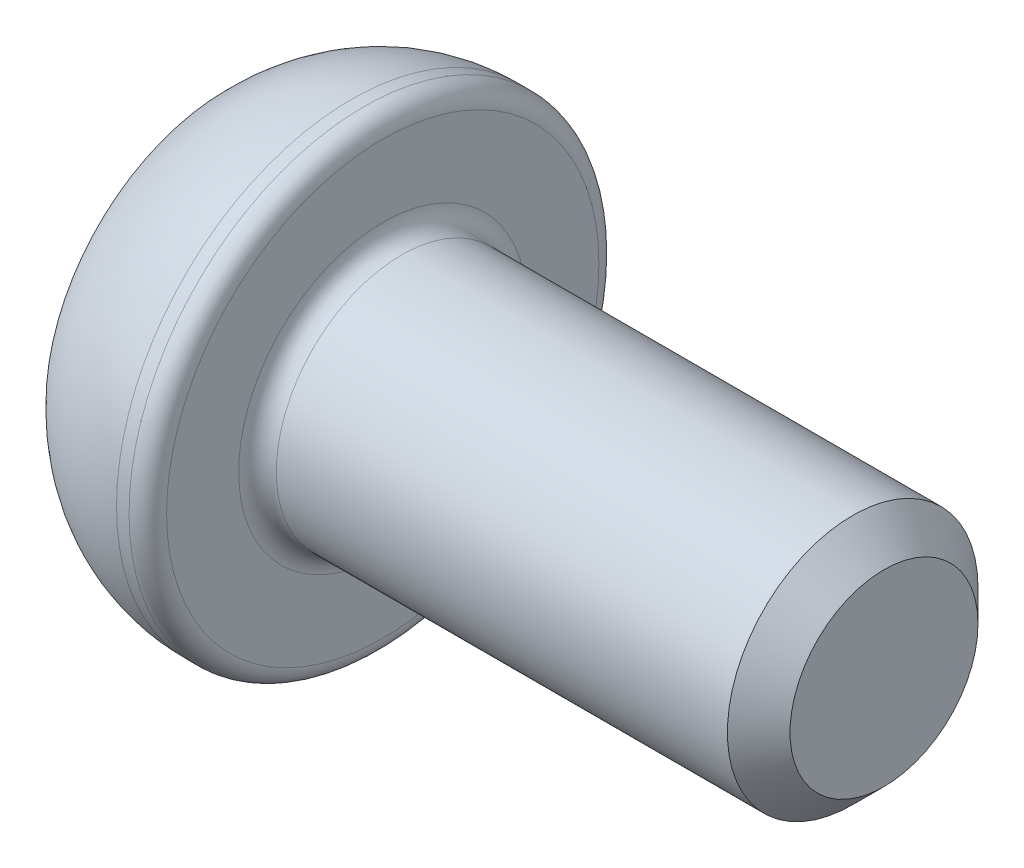
SolidWorks part; units mm, degrees
ref_plane "Спереди" through (0, 0, 0) normal (0, 0, 1) x (1, 0, 0)
ref_plane "Сверху" through (0, 0, 0) normal (0, 1, 0) x (1, 0, 0)
ref_plane "Справа" through (0, 0, 0) normal (1, 0, 0) x (0, 0, -1)
sketch "Эскиз1" plane through (0, 0, 0) normal (0, 0, 1) x (1, 0, 0)
  line L0 (0, 0) -> (0, 2.875)
  line L1 (2, 3.75) -> (2.5, 3.75)
  line L2 (2.5, 3.75) -> (2.5, 2)
  line L3 (2.5, 2) -> (10.5, 2)
  line L4 (10.5, 2) -> (10.5, 0)
  line L5 (10.5, 0) -> (0, 0) construction
  line L6 (0, 0) -> (10.5, 0)
  arc A0 (0, 2.875) -> (2, 3.75) centre (2, 1.0268) cw
  point P9 (2.5, 2.875)
  dimension "D1" = 0.5
  dimension "D2" = 4
  dimension "D3" = 7.5
  dimension "D5" = 2.5
  dimension "D6" = 8
revolve "Повернуть1" add sketch "Эскиз1" angle 360 about L5
cosmetic thread "Условное изображение резьбы1" parameters "D2"=3.22
sketch "Эскиз2" plane through (0, 0, 0) normal (-1, 0, 0) x (0, 0, 1)
  line L1 (0.7217, 1.25) -> (-0.7217, 1.25)
  line L2 (-0.7217, 1.25) -> (-1.4434, 0)
  line L3 (-1.4434, 0) -> (-0.7217, -1.25)
  line L4 (-0.7217, -1.25) -> (0.7217, -1.25)
  line L5 (0.7217, -1.25) -> (1.4434, 0)
  line L6 (1.4434, 0) -> (0.7217, 1.25)
  circle A0 centre (0, 0) radius 1.25 construction
  dimension "D1" = 2.5
extrude "Вырез-Вытянуть1" cut sketch "Эскиз2" against normal blind 1.5
fillet "Скругление1" radius 0.3 2 edges at (2.5, 0, -2) (2.5, 0, -3.75)
chamfer "Фаска1" distance 0.5 angle 45 1 edges at (10.5, 0, -2)
